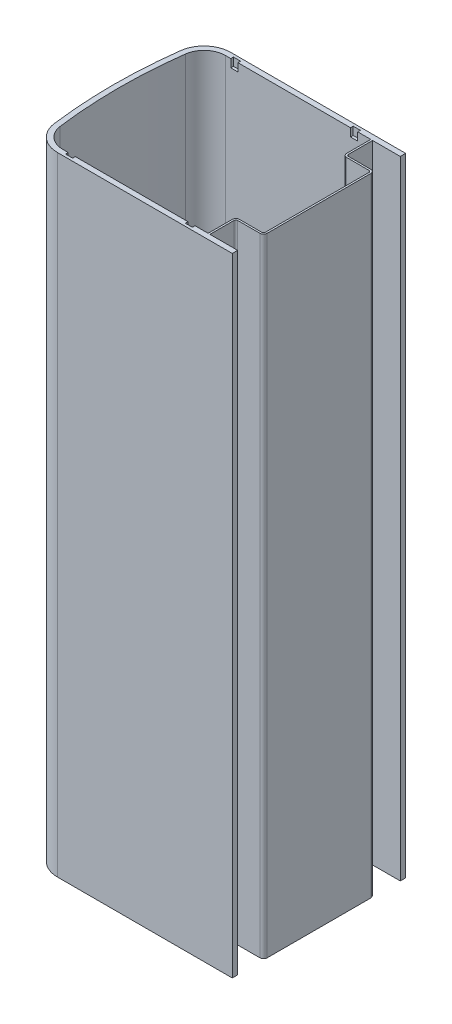
SolidWorks part; units mm, degrees
material "PVC Rigid"
ref_plane "Front Plane" through (0, 0, 0) normal (0, 0, 1) x (1, 0, 0)
ref_plane "Top Plane" through (0, 0, 0) normal (0, 1, 0) x (1, 0, 0)
ref_plane "Right Plane" through (0, 0, 0) normal (1, 0, 0) x (0, 0, -1)
sketch "Sketch1" plane through (0, 0, 0) normal (0, 1, 0) x (1, 0, 0)
  line L0 (-257.8328, 48.5) -> (-160, 48.5)
  line L1 (-257.8328, -48.5) -> (-160, -48.5)
  line L2 (-257.8328, 45.5) -> (-160, 45.5)
  line L3 (-160, 45.5) -> (-160, 48.5)
  line L4 (-257.8328, -45.5) -> (-160, -45.5)
  line L5 (-160, -45.5) -> (-160, -48.5)
  arc A0 (-272.7078, 35.4327) -> (-272.7078, -35.4327) centre (0, 0) ccw
  arc A1 (-257.8328, 48.5) -> (-272.7078, 35.4327) centre (-257.8328, 33.5) ccw
  arc A2 (-272.7078, -35.4327) -> (-257.8328, -48.5) centre (-257.8328, -33.5) ccw
  arc A3 (-269.7328, 35.0462) -> (-269.7328, -35.0462) centre (0, 0) ccw
  arc A4 (-257.8328, 45.5) -> (-269.7328, 35.0462) centre (-257.8328, 33.5) ccw
  arc A5 (-269.7328, -35.0462) -> (-257.8328, -45.5) centre (-257.8328, -33.5) ccw
  point P17 (-160, -47)
  dimension "D1" = 550
  dimension "D3" = 15
  dimension "D4" = 15
  dimension "D5" = 3
  dimension "D7" = 544
  dimension "D8" = 24
  dimension "D9" = 24
  dimension "D10" = 160
  dimension "D2" = 97
  dimension "D6" = 3
extrude "Boss-Extrude1" add sketch "Sketch1" along normal blind 351.07
sketch "Sketch2" plane through (0, 0, -45.5) normal (0, 0, 1) x (1, 0, 0)
  line L0 (-257.8328, 351.07) -> (-160, 351.07) construction
  line L1 (-250.8328, 346.57) -> (-254.8328, 346.57)
  line L2 (-250.8328, 346.57) -> (-250.8328, 355.57)
  line L3 (-250.8328, 355.57) -> (-254.8328, 355.57)
  line L4 (-254.8328, 346.57) -> (-254.8328, 355.57)
  line L5 (-250.8328, 346.57) -> (-254.8328, 355.57) construction
  line L6 (-250.8328, 355.57) -> (-254.8328, 346.57) construction
  line L7 (-257.8328, 351.07) -> (-257.8328, 0) construction
  line L8 (-183.8328, 346.57) -> (-187.8328, 346.57)
  line L9 (-183.8328, 346.57) -> (-183.8328, 355.57)
  line L10 (-183.8328, 355.57) -> (-187.8328, 355.57)
  line L11 (-187.8328, 346.57) -> (-187.8328, 355.57)
  line L12 (-183.8328, 346.57) -> (-187.8328, 355.57) construction
  line L13 (-183.8328, 355.57) -> (-187.8328, 346.57) construction
  point P0 (-252.8328, 351.07)
  point P7 (-185.8328, 351.07)
  dimension "D1" = 4
  dimension "D2" = 4
  dimension "D3" = 9
  dimension "D4" = 9
  dimension "D5" = 3
  dimension "D6" = 63
extrude "Cut-Extrude1" cut sketch "Sketch2" against normal blind 1.5
ref_plane "Plane1" through (0, 0, 0) normal (0, 0, 1) x (1, 0, 0)
mirror "Mirror1" about plane through (0, 0, 0) normal (0, 0, 1) of "Cut-Extrude1"
sketch "Sketch3" plane through (0, 351.07, 0) normal (0, 1, 0) x (1, 0, 0)
  line L0 (-183.8328, 45.5) -> (-160, 45.5) construction
  line L1 (-238.4037, 0) -> (-124.2452, 0) construction
  line L2 (-176.5, -45.5) -> (-176.5, -32)
  line L3 (-175.5, 45.5) -> (-176.5, 45.5)
  line L4 (-175.5, 45.5) -> (-175.5, 32)
  line L6 (-176.5, 45.5) -> (-176.5, 32)
  line L7 (-160, -45.5) -> (-183.8328, -45.5) construction
  line L8 (-160, 45.5) -> (-160, 48.5) construction
  line L9 (-160, 29) -> (-160, -29)
  line L10 (-161, -29) -> (-161, 29)
  line L11 (-174.5, 31) -> (-162, 31)
  line L12 (-174.5, 30) -> (-162, 30)
  line L13 (-175.5, -45.5) -> (-175.5, -32)
  line L14 (-174.5, -31) -> (-162, -31)
  line L15 (-174.5, -30) -> (-162, -30)
  line L16 (-175.5, -45.5) -> (-176.5, -45.5)
  line L17 (-160, -48.5) -> (-160, -45.5) construction
  arc A0 (-160, 29) -> (-162, 31) centre (-162, 29) ccw
  arc A1 (-161, 29) -> (-162, 30) centre (-162, 29) ccw
  arc A2 (-174.5, 30) -> (-176.5, 32) centre (-174.5, 32) cw
  arc A3 (-174.5, 31) -> (-175.5, 32) centre (-174.5, 32) cw
  arc A4 (-174.5, -30) -> (-176.5, -32) centre (-174.5, -32) ccw
  arc A5 (-160, -29) -> (-162, -31) centre (-162, -29) cw
  arc A6 (-174.5, -31) -> (-175.5, -32) centre (-174.5, -32) ccw
  arc A7 (-161, -29) -> (-162, -30) centre (-162, -29) cw
  point P10 (-160, 47)
  dimension "D6" = 2
  dimension "D7" = 1
  dimension "D8" = 2
  dimension "D9" = 1
  dimension "D12" = 2
  dimension "D13" = 2
  dimension "D14" = 1
  dimension "D15" = 1
  dimension "D1" = 1
  dimension "D2" = 15.5
  dimension "D3" = 1
  dimension "D4" = 1
  dimension "D5" = 15.5
  dimension "D10" = 1
  dimension "D11" = 15.5
extrude "Boss-Extrude2" add sketch "Sketch3" against normal up to surface (351.07 mm away) up to face at (-230.803, 0, 0)
